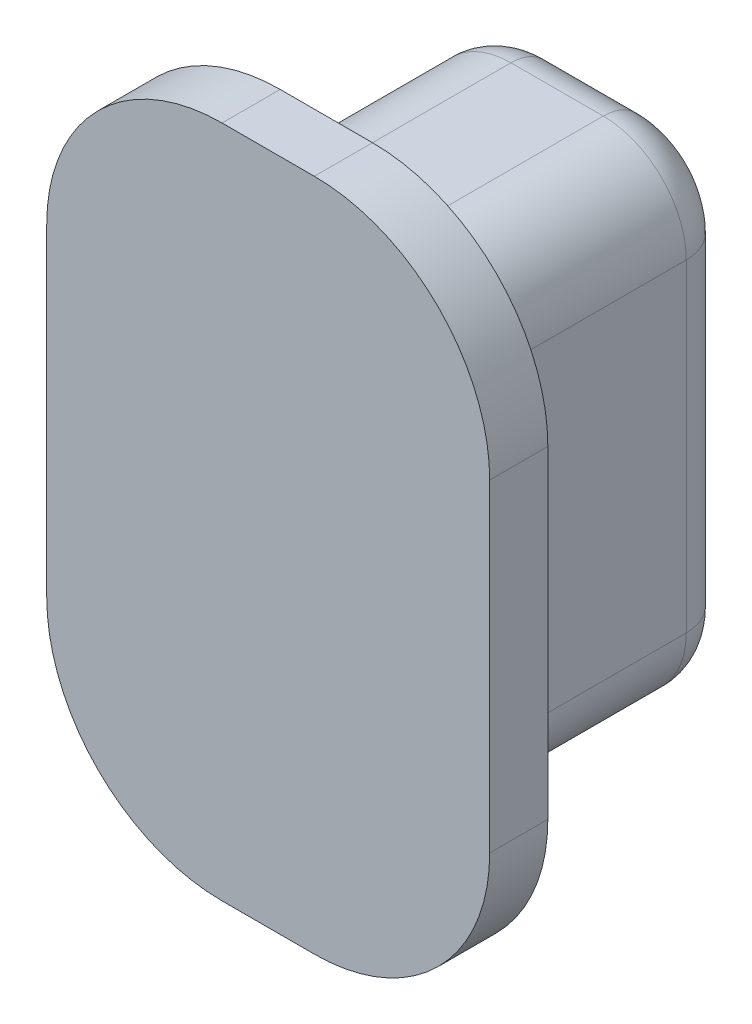
SolidWorks part; units mm, degrees
ref_plane "Front Plane" through (0, 0, 0) normal (0, 0, 1) x (1, 0, 0)
ref_plane "Top Plane" through (0, 0, 0) normal (0, 1, 0) x (1, 0, 0)
ref_plane "Right Plane" through (0, 0, 0) normal (1, 0, 0) x (0, 0, -1)
sketch "Sketch1" plane through (0, 0, 0) normal (0, 0, 1) x (1, 0, 0)
  line L0 (-3.5, 18.3) -> (-2.5, 18.3) construction
  line L1 (-4.5, 22.8) -> (-4.5, 19.3) construction
  line L2 (-1.5, 19.3) -> (-1.5, 22.8) construction
  line L3 (-2.5, 23.8) -> (-3.5, 23.8) construction
  line L4 (-3.5, 18.3) -> (-2.5, 18.3) construction
  line L5 (-2.5, 23.8) -> (-3.5, 23.8) construction
  line L6 (-1.5, 19.3) -> (-1.5, 22.8) construction
  line L7 (-4.5, 22.8) -> (-4.5, 19.3) construction
  line L8 (-3.5, 18.4) -> (-2.5, 18.4)
  line L9 (-1.6, 19.3) -> (-1.6, 22.8)
  line L10 (-2.5, 23.7) -> (-3.5, 23.7)
  line L11 (-4.4, 22.8) -> (-4.4, 19.3)
  arc A0 (-3.5, 23.8) -> (-4.5, 22.8) centre (-3.5, 22.8) ccw construction
  arc A1 (-4.5, 19.3) -> (-3.5, 18.3) centre (-3.5, 19.3) ccw construction
  arc A2 (-2.5, 18.3) -> (-1.5, 19.3) centre (-2.5, 19.3) ccw construction
  arc A3 (-1.5, 22.8) -> (-2.5, 23.8) centre (-2.5, 22.8) ccw construction
  arc A4 (-1.5, 22.8) -> (-2.5, 23.8) centre (-2.5, 22.8) ccw construction
  arc A5 (-2.5, 18.3) -> (-1.5, 19.3) centre (-2.5, 19.3) ccw construction
  arc A6 (-4.5, 19.3) -> (-3.5, 18.3) centre (-3.5, 19.3) ccw construction
  arc A7 (-3.5, 23.8) -> (-4.5, 22.8) centre (-3.5, 22.8) ccw construction
  arc A8 (-2.5, 18.4) -> (-1.6, 19.3) centre (-2.5, 19.3) ccw
  arc A9 (-1.6, 22.8) -> (-2.5, 23.7) centre (-2.5, 22.8) ccw
  arc A10 (-3.5, 23.7) -> (-4.4, 22.8) centre (-3.5, 22.8) ccw
  arc A11 (-4.4, 19.3) -> (-3.5, 18.4) centre (-3.5, 19.3) ccw
  point P5 (-3, 18.4)
  point P19 (-3, 23.7)
  point P26 (-4.4, 21.05)
  point P27 (-1.6, 21.05)
  dimension "D1" = 0.1
extrude "Boss-Extrude1" add sketch "Sketch1" against normal offset from surface (3 mm away) 0.5 contours L4 A5 L6 A4 L5 A7 L7 A6
sketch "Sketch2" plane through (0, 0, 0) normal (0, 0, 1) x (1, 0, 0)
  line L0 (-3.5, 17.4) -> (-2.5, 17.4)
  line L1 (-0.6, 19.3) -> (-0.6, 22.8)
  line L2 (-2.5, 24.7) -> (-3.5, 24.7)
  line L3 (-5.4, 22.8) -> (-5.4, 19.3)
  line L4 (-3.5, 18.4) -> (-2.5, 18.4)
  line L5 (-1.6, 19.3) -> (-1.6, 22.8)
  line L6 (-2.5, 23.7) -> (-3.5, 23.7)
  line L7 (-4.4, 22.8) -> (-4.4, 19.3)
  line L8 (-3.5, 18.4) -> (-2.5, 18.4) construction
  line L9 (-1.6, 19.3) -> (-1.6, 22.8) construction
  line L10 (-2.5, 23.7) -> (-3.5, 23.7) construction
  line L11 (-4.4, 22.8) -> (-4.4, 19.3) construction
  arc A0 (-5.4, 19.3) -> (-3.5, 17.4) centre (-3.5, 19.3) ccw
  arc A1 (-2.5, 17.4) -> (-0.6, 19.3) centre (-2.5, 19.3) ccw
  arc A2 (-0.6, 22.8) -> (-2.5, 24.7) centre (-2.5, 22.8) ccw
  arc A3 (-3.5, 24.7) -> (-5.4, 22.8) centre (-3.5, 22.8) ccw
  arc A4 (-4.4, 19.3) -> (-3.5, 18.4) centre (-3.5, 19.3) ccw
  arc A5 (-2.5, 18.4) -> (-1.6, 19.3) centre (-2.5, 19.3) ccw
  arc A6 (-1.6, 22.8) -> (-2.5, 23.7) centre (-2.5, 22.8) ccw
  arc A7 (-3.5, 23.7) -> (-4.4, 22.8) centre (-3.5, 22.8) ccw
  arc A8 (-4.4, 19.3) -> (-3.5, 18.4) centre (-3.5, 19.3) ccw construction
  arc A9 (-2.5, 18.4) -> (-1.6, 19.3) centre (-2.5, 19.3) ccw construction
  arc A10 (-1.6, 22.8) -> (-2.5, 23.7) centre (-2.5, 22.8) ccw construction
  arc A11 (-3.5, 23.7) -> (-4.4, 22.8) centre (-3.5, 22.8) ccw construction
  dimension "D1" = 0
  dimension "D2" = 1
extrude "Boss-Extrude2" add sketch "Sketch2" along normal offset from surface (0.63 mm away) 0.1
fillet "Fillet1" radius 0.5 8 edges at (-3, 18.4, -3) (-1.8636, 18.6636, -3) (-1.6, 21.05, -3) (-1.8636, 23.4364, -3) (-3, 23.7, -3) (-4.1364, 23.4364, -3) (-4.4, 21.05, -3) (-4.1364, 18.6636, -3)
